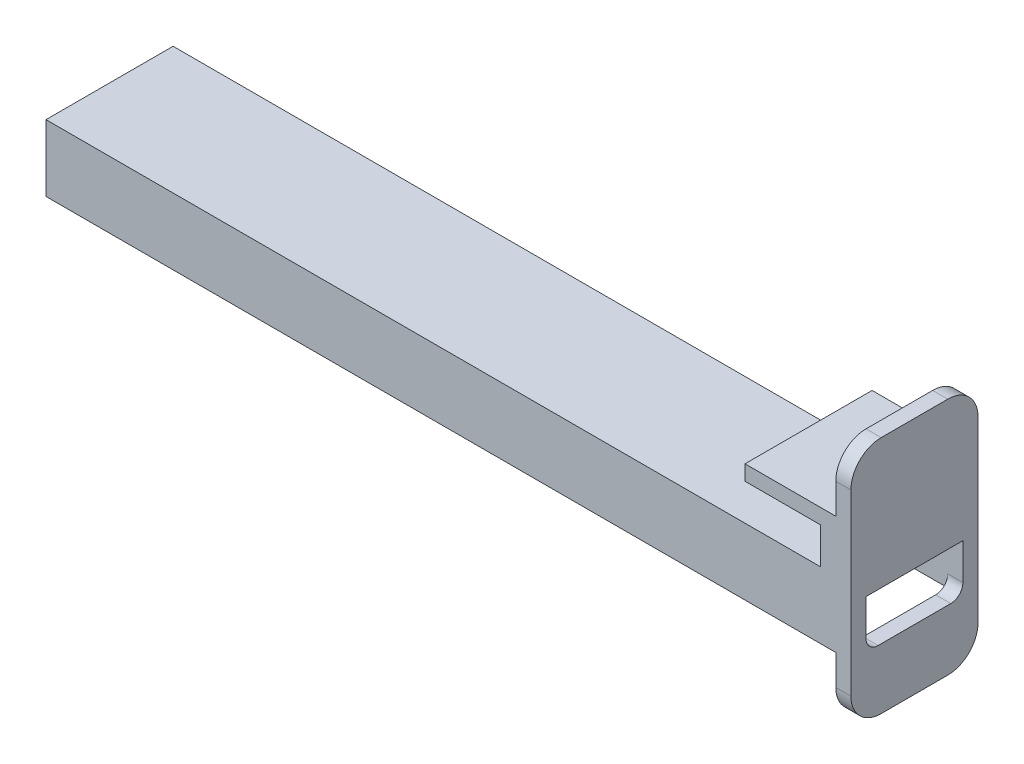
SolidWorks part; units mm, degrees
ref_plane "Front Plane" through (0, 0, 0) normal (0, 0, 1) x (1, 0, 0)
ref_plane "Top Plane" through (0, 0, 0) normal (0, 1, 0) x (1, 0, 0)
ref_plane "Right Plane" through (0, 0, 0) normal (1, 0, 0) x (0, 0, -1)
sketch "Sketch1" plane through (0, 0, 0) normal (0, 1, 0) x (1, 0, 0)
  line L1 (-53.6154, 15.4615) -> (74.3846, 15.4615)
  line L2 (-53.6154, 15.4615) -> (-53.6154, -5.5385)
  line L3 (-53.6154, -5.5385) -> (74.3846, -5.5385)
  line L4 (74.3846, 15.4615) -> (74.3846, -5.5385)
  line L5 (-53.6154, 12.9615) -> (74.3846, 12.9615)
  line L6 (-53.6154, 12.9615) -> (-53.6154, -3.0385)
  line L7 (-53.6154, -3.0385) -> (74.3846, -3.0385)
  line L8 (74.3846, 12.9615) -> (74.3846, -3.0385)
  dimension "D1" = 21
  dimension "D2" = 16
  dimension "D3" = 2.5
  dimension "D4" = 128
extrude "Boss-Extrude1" add sketch "Sketch1" along normal blind 8 contours L2 L5 L4 L1 | L7 L2 L3 L4
sketch "Sketch2" plane through (0, 8, 0) normal (0, 1, 0) x (1, 0, 0)
  line L1 (-53.6154, 15.4615) -> (74.3846, 15.4615)
  line L2 (-53.6154, 15.4615) -> (-53.6154, -5.5385)
  line L3 (-53.6154, -5.5385) -> (74.3846, -5.5385)
  line L4 (74.3846, 15.4615) -> (74.3846, -5.5385)
extrude "Boss-Extrude2" add sketch "Sketch2" along normal blind 3
sketch "Sketch3" plane through (74.3846, 0, 0) normal (1, 0, 0) x (0, 0, -1)
  line L0 (15.4615, 11) -> (15.4615, 0) construction
  line L1 (-5.5385, 0) -> (15.4615, 0)
  line L2 (-5.5385, 0) -> (-5.5385, 17)
  line L3 (-5.5385, 17) -> (15.4615, 17)
  line L4 (15.4615, 0) -> (15.4615, 17)
  line L5 (-5.5385, 11) -> (15.4615, 11) construction
  dimension "D1" = 0
  dimension "D2" = 6
extrude "Boss-Extrude3" add sketch "Sketch3" along normal blind 2.5
sketch "Sketch4" plane through (0, 17, 0) normal (0, 1, 0) x (1, 0, 0)
  line L0 (76.8846, -5.5385) -> (74.3846, -5.5385) construction
  line L1 (76.8846, 15.4615) -> (61.8846, 15.4615)
  line L2 (76.8846, 15.4615) -> (76.8846, -5.5385)
  line L3 (76.8846, -5.5385) -> (61.8846, -5.5385)
  line L4 (61.8846, 15.4615) -> (61.8846, -5.5385)
  dimension "D1" = 0
  dimension "D2" = 15
extrude "Boss-Extrude4" add sketch "Sketch4" along normal blind 2.5
sketch "Sketch5" plane through (76.8846, 0, 0) normal (1, 0, 0) x (0, 0, -1)
  line L0 (15.4615, 0) -> (15.4615, 19.5) construction
  line L1 (-5.5385, 29.5) -> (15.4615, 29.5)
  line L2 (-5.5385, 29.5) -> (-5.5385, -10)
  line L3 (-5.5385, -10) -> (15.4615, -10)
  line L4 (15.4615, 29.5) -> (15.4615, -10)
  line L5 (-5.5385, 19.5) -> (-5.5385, 0) construction
  line L6 (-5.5385, 0) -> (15.4615, 0) construction
  line L7 (-5.5385, 19.5) -> (15.4615, 19.5) construction
  dimension "D1" = 0
  dimension "D2" = 0
  dimension "D3" = 10
  dimension "D4" = 10
extrude "Boss-Extrude5" add sketch "Sketch5" along normal blind 2.5
fillet "Fillet1" radius 5 4 edges at (78.1346, 29.5, -15.4615) (78.1346, 29.5, 5.5385) (78.1346, -10, 5.5385) (78.1346, -10, -15.4615)
sketch "Sketch6" plane through (74.3846, 0, 0) normal (-1, 0, 0) x (0, 0, 1)
  line L4 (3.0385, 0) -> (3.0385, 8)
  line L5 (3.0385, 8) -> (-12.9615, 8)
  line L6 (-12.9615, 8) -> (-12.9615, 0)
  line L7 (-12.9615, 0) -> (3.0385, 0)
  line L8 (3.0385, 0) -> (3.0385, 8)
  line L9 (3.0385, 8) -> (-12.9615, 8)
  line L10 (-12.9615, 8) -> (-12.9615, 0)
  line L11 (-12.9615, 0) -> (3.0385, 0)
  dimension "D1" = 0
extrude "Cut-Extrude1" cut sketch "Sketch6" against normal blind 18.5
fillet "Fillet2" radius 2 2 edges at (78.1346, 0, -12.9615) (78.1346, 0, 3.0385)
